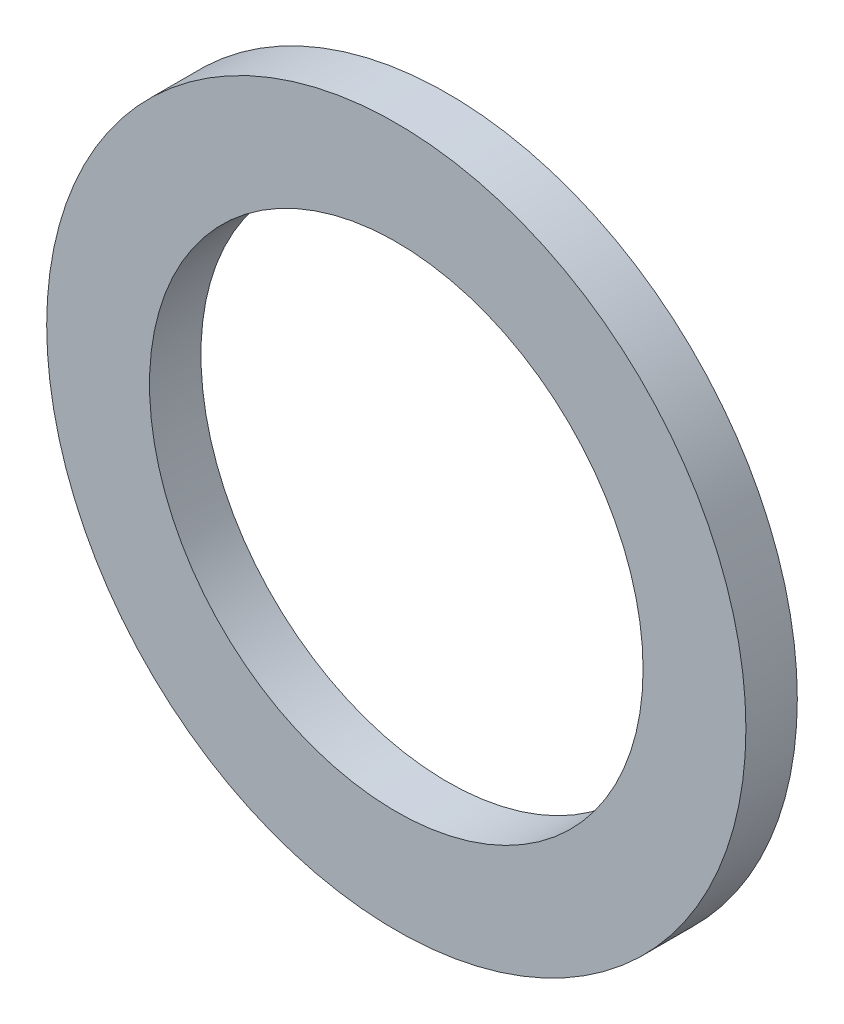
SolidWorks part; units mm, degrees
ref_plane "Front Plane" through (0, 0, 0) normal (0, 0, 1) x (1, 0, 0)
ref_plane "Top Plane" through (0, 0, 0) normal (0, 1, 0) x (1, 0, 0)
ref_plane "Right Plane" through (0, 0, 0) normal (1, 0, 0) x (0, 0, -1)
sketch "Sketch1" plane through (0, 0, 0) normal (0, 0, 1) x (1, 0, 0)
  circle A0 centre (0, 0) radius 15.24
  circle A1 centre (0, 0) radius 21.59
  dimension "D1" = 30.48
  dimension "D2" = 6.35
extrude "Boss-Extrude1" add sketch "Sketch1" along normal blind 3.175
